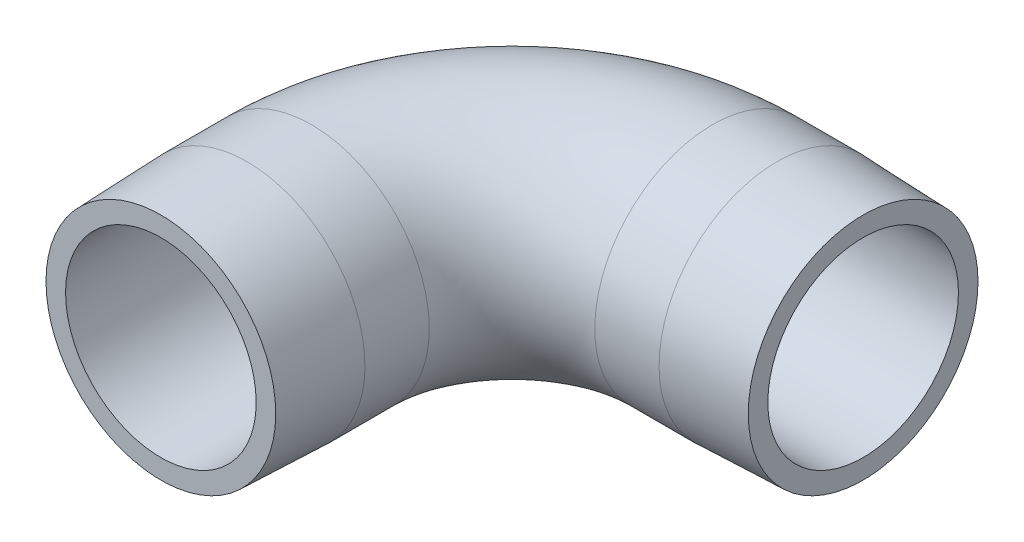
SolidWorks part; units mm, degrees
ref_plane "Front Plane" through (0, 0, 0) normal (0, 0, 1) x (1, 0, 0)
ref_plane "Top Plane" through (0, 0, 0) normal (0, 1, 0) x (1, 0, 0)
ref_plane "Right Plane" through (0, 0, 0) normal (1, 0, 0) x (0, 0, -1)
sketch "Sketch1" plane through (0, 0, 0) normal (0, 1, 0) x (1, 0, 0)
  line L0 (0, 0) -> (0, 15)
  line L1 (20, 35) -> (35, 35)
  arc A0 (0, 15) -> (20, 35) centre (20, 15) cw
  point P6 (0, 35)
  dimension "D3" = 20
  dimension "D1" = 35
  dimension "D2" = 35
sketch "Sketch2" plane through (0, 0, 0) normal (0, 0, 1) x (1, 0, 0)
  circle A1 centre (0, 0) radius 11.75
  circle A2 centre (0, 0) radius 9.5
  dimension "D1" = 19
  dimension "D2" = 23.5
sweep "Sweep1" add profiles "Sketch2" path "Sketch1"
sketch "Sketch40" plane through (0, 0, 0) normal (0, 0, 1) x (1, 0, 0)
  circle A0 centre (0, 0) radius 11.45
  dimension "D1" = 22.9
extrude "Cut-Extrude2" cut sketch "Sketch40" against normal blind 15 draft 2 flip side to cut
sketch "Sketch41" plane through (35, 0, 0) normal (1, 0, 0) x (0, 0, -1)
  circle A0 centre (35, 0) radius 11.45
  dimension "D1" = 22.9
extrude "Cut-Extrude3" cut sketch "Sketch41" against normal blind 15 draft 2 flip side to cut
